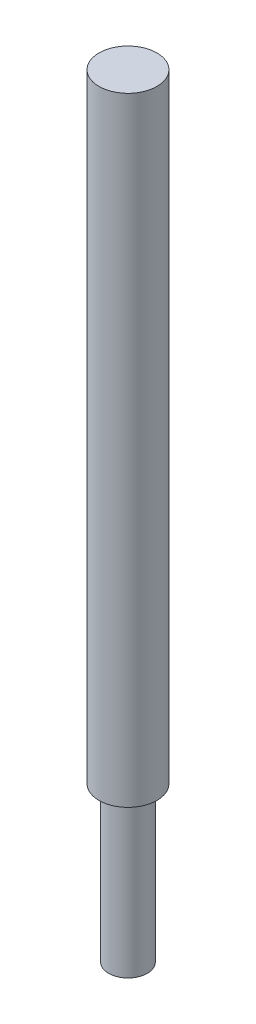
SolidWorks part; units mm, degrees
ref_plane "Front Plane" through (0, 0, 0) normal (0, 0, 1) x (1, 0, 0)
ref_plane "Top Plane" through (0, 0, 0) normal (0, 1, 0) x (1, 0, 0)
ref_plane "Right Plane" through (0, 0, 0) normal (1, 0, 0) x (0, 0, -1)
sketch "Sketch1" plane through (0, 0, 0) normal (0, 1, 0) x (1, 0, 0)
  circle A0 centre (0, 0) radius 3.175
  dimension "D1" = 6.35
extrude "Boss-Extrude1" add sketch "Sketch1" along normal blind 25.4
sketch "Sketch2" plane through (0, 25.4, 0) normal (0, 1, 0) x (1, 0, 0)
  circle A0 centre (0, 0) radius 4.7625
extrude "Boss-Extrude2" add sketch "Sketch2" along normal blind 101.6
